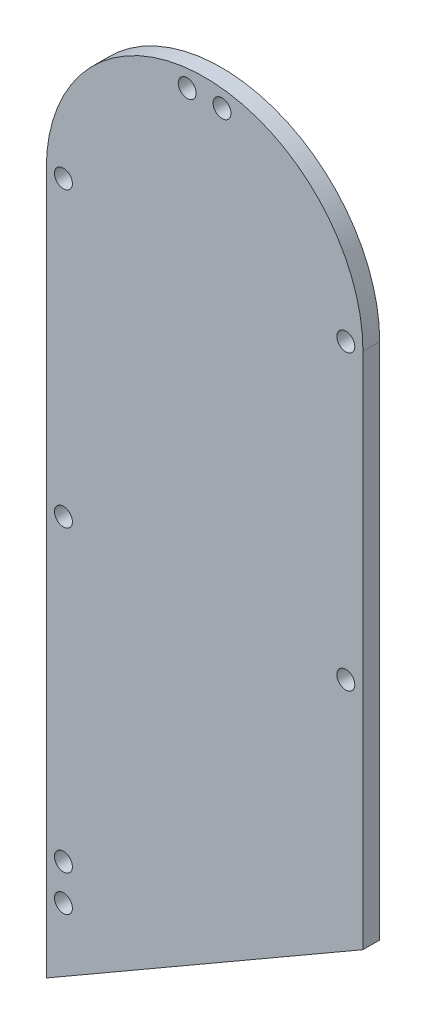
SolidWorks part; units mm, degrees
ref_plane "Front Plane" through (0, 0, 0) normal (0, 0, 1) x (1, 0, 0)
ref_plane "Top Plane" through (0, 0, 0) normal (0, 1, 0) x (1, 0, 0)
ref_plane "Right Plane" through (0, 0, 0) normal (1, 0, 0) x (0, 0, -1)
sketch "Sketch2" plane through (0, 0, 0) normal (0, 0, 1) x (1, 0, 0)
  line L0 (54.5827, -59.5829) -> (54.5827, 171.3946)
  line L1 (-5.4173, 171.3946) -> (-5.4173, -59.5829)
  arc A0 (-5.4173, -59.5829) -> (54.5827, -59.5829) centre (24.5827, -59.5829) ccw
  arc A1 (54.5827, 171.3946) -> (-5.4173, 171.3946) centre (24.5827, 171.3946) ccw
  circle A2 centre (27.8827, 197.9403) radius 1.7
  circle A3 centre (-2.1673, -59.5829) radius 1.7
  circle A4 centre (5.6676, -78.498) radius 1.7
  circle A5 centre (21.1827, -86.116) radius 1.7
  circle A6 centre (51.3327, 171.3946) radius 1.7
  circle A9 centre (-2.1673, 59.3059) radius 1.7
  circle A10 centre (27.9827, -86.116) radius 1.7
  circle A12 centre (-2.1673, 171.3946) radius 1.7
  circle A13 centre (51.3327, 115.9059) radius 1.7
  circle A14 centre (-2.1673, 115.9059) radius 1.7
  circle A16 centre (43.4978, -78.498) radius 1.7
  circle A17 centre (51.3327, -59.5829) radius 1.7
  circle A18 centre (51.3327, -34.0941) radius 1.7
  circle A19 centre (-2.1673, -34.0941) radius 1.7
  circle A20 centre (51.3327, -4.0941) radius 1.7
  circle A21 centre (-2.1673, -4.0941) radius 1.7
  circle A22 centre (51.3327, 25.9059) radius 1.7
  circle A23 centre (-2.1673, 25.9059) radius 1.7
  circle A26 centre (21.2827, 197.9403) radius 1.7
  circle A27 centre (51.3327, 52.5059) radius 1.7
  circle A28 centre (51.3327, 59.3059) radius 1.7
  circle A29 centre (-2.1673, 52.5059) radius 1.7
  point P16 (0, 0)
  point P62 (0, 0)
extrude "Boss-Extrude1" add sketch "Sketch2" along normal blind 3.175
sketch "Sketch3" plane through (0, 0, 3.175) normal (0, 0, 1) x (1, 0, 0)
  line L0 (-23.1786, 28.3308) -> (72.344, 83.4809)
  line L1 (-5.4173, 55.9059) -> (54.5827, 55.9059) construction
  line L2 (-5.4173, 171.3946) -> (-5.4173, -59.5829) construction
  line L3 (54.5827, -59.5829) -> (54.5827, 171.3946) construction
  line L4 (-23.1786, 28.3308) -> (-23.1786, -133.0465)
  line L5 (-23.1786, -133.0465) -> (72.344, -133.0465)
  line L6 (72.344, -133.0465) -> (72.344, 83.4809)
  point P8 (24.5827, 55.9059)
  point P9 (24.5827, 55.9059)
  dimension "D1" = 30
extrude "Cut-Extrude1" cut sketch "Sketch3" against normal through all
